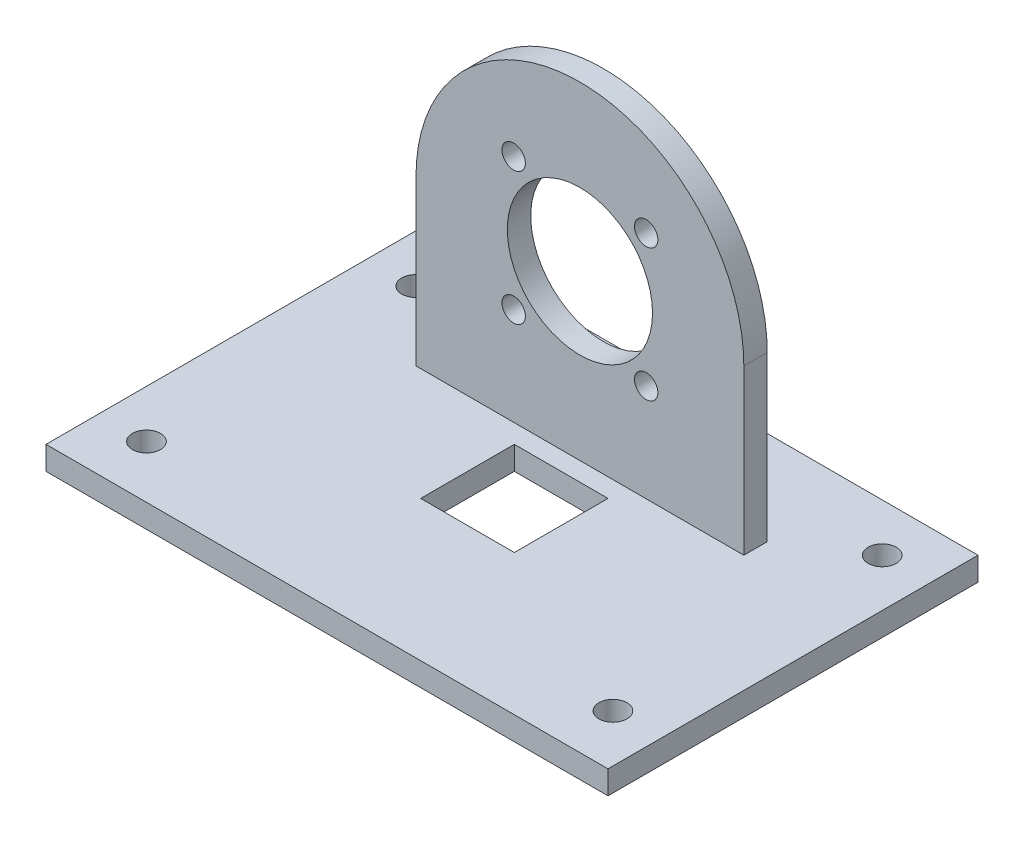
SolidWorks part; units mm, degrees
material "Alloy Steel"
ref_plane "Front Plane" through (0, 0, 0) normal (0, 0, 1) x (1, 0, 0)
ref_plane "Top Plane" through (0, 0, 0) normal (0, 1, 0) x (1, 0, 0)
ref_plane "Right Plane" through (0, 0, 0) normal (1, 0, 0) x (0, 0, -1)
sketch "Sketch1" plane through (0, 0, 0) normal (0, 1, 0) x (1, 0, 0)
  line L0 (0, -114.1661) -> (0, 132.8372) construction
  line L1 (135.7044, 0) -> (-145.1402, 0) construction
  line L2 (-35, -40) -> (-20, -40)
  line L3 (-35, 19) -> (35, 19) construction
  line L4 (-35, 19) -> (-35, -40) construction
  line L5 (-20, -70) -> (20, -70)
  line L6 (35, 19) -> (35, -40) construction
  line L7 (-20, -40) -> (-20, -70)
  line L8 (35, -40) -> (20, -40)
  line L9 (20, -40) -> (20, -70)
  line L10 (-35, -40) -> (-60, -40)
  line L11 (-60, -40) -> (-60, 39)
  line L12 (-60, 39) -> (60, 39)
  line L13 (60, 39) -> (60, -40)
  line L14 (60, -40) -> (35, -40)
  circle A0 centre (0, 0) radius 57.5 construction
  circle A1 centre (0, 0) radius 2.5 construction
  circle A2 centre (0, 57.5) radius 3 construction
  circle A3 centre (49.7965, 28.75) radius 3
  circle A4 centre (49.7965, -28.75) radius 3
  circle A5 centre (0, -57.5) radius 3
  circle A6 centre (-49.7965, -28.75) radius 3
  circle A7 centre (-49.7965, 28.75) radius 3
  point P22 (0, 0)
  dimension "D1" = 115
  dimension "D2" = 6
  dimension "D3" = 5
  dimension "D4" = 6
  dimension "D5" = 70
  dimension "D6" = 19
  dimension "D7" = 35
  dimension "D8" = 25
  dimension "D9" = 30
  dimension "D10" = 15
  dimension "D11" = 30
  dimension "D12" = 15
  dimension "D13" = 25
  dimension "D14" = 20
extrude "Boss-Extrude1" add sketch "Sketch1" along normal blind 5
sketch "Sketch2" plane through (0, 5, 0) normal (0, 1, 0) x (1, 0, 0)
  line L1 (-35, 19) -> (35, 19)
  line L2 (-35, 19) -> (-35, 14)
  line L3 (-35, 14) -> (35, 14)
  line L4 (35, 14) -> (35, 19)
  dimension "D1" = 70
  dimension "D2" = 5
  dimension "D3" = 19
extrude "Boss-Extrude2" add sketch "Sketch2" along normal blind 70
sketch "Sketch3" plane through (0, 0, -19) normal (0, 0, -1) x (-1, 0, 0)
  line L0 (-35, 75) -> (35, 75) construction
  line L1 (35, 75) -> (35, 5) construction
  line L2 (-35, 75) -> (-35, 5) construction
  line L3 (35, 75) -> (35, 40)
  line L4 (-35, 75) -> (-35, 40)
  line L5 (-35, 75) -> (35, 75)
  arc A0 (35, 40) -> (-35, 40) centre (0, 40) ccw
  line M2 (35, 5) -> (35, 75)
  line M3 (35, 75) -> (-35, 75)
  line M4 (-35, 75) -> (-35, 5)
  dimension "D1" = 70
extrude "Cut-Extrude1" cut sketch "Sketch3" against normal blind 20 contours A0 L5 M4 | A0 M2 M3
sketch "Sketch4" plane through (0, 0, -14) normal (0, 0, 1) x (1, 0, 0)
  circle A0 centre (0, 40) radius 15.5
  dimension "D1" = 31
extrude "Cut-Extrude2" cut sketch "Sketch4" against normal blind 10
sketch "Sketch8" plane through (0, 0, 0) normal (0, -1, 0) x (1, 0, 0)
  line L0 (0, 70) -> (0, 0) construction
  line L1 (-20, 70) -> (20, 70) construction
  line L3 (-10, -10) -> (10, -10)
  line L4 (-10, -10) -> (-10, 10)
  line L5 (-10, 10) -> (10, 10)
  line L6 (10, -10) -> (10, 10)
  line L7 (-10, -10) -> (10, 10) construction
  line L8 (-10, 10) -> (10, -10) construction
  dimension "D1" = 70
  dimension "D2" = 20
  dimension "D3" = 20
extrude "Cut-Extrude6" cut sketch "Sketch8" against normal up to surface (28.1573 mm away)
sketch "Sketch9" plane through (0, 0, 70) normal (0, 0, 1) x (1, 0, 0)
  line L1 (-20, 5) -> (20, 5)
  line L2 (-20, 5) -> (-20, 0)
  line L3 (-20, 0) -> (20, 0)
  line L4 (20, 5) -> (20, 0)
extrude "Cut-Extrude7" cut sketch "Sketch9" against normal up to surface (30 mm away) up to face at (40, 2.5, 40)
sketch "Sketch10" plane through (0, 0, -19) normal (0, 0, -1) x (-1, 0, 0)
  line L0 (0, 40) -> (0, 73.9404) construction
  line L1 (0, 40) -> (33.32, 73.32) construction
  circle A0 centre (0, 40) radius 20 construction
  circle A1 centre (14.1421, 54.1421) radius 2.5
  circle A2 centre (14.1421, 25.8579) radius 2.5
  circle A3 centre (-14.1421, 25.8579) radius 2.5
  circle A4 centre (-14.1421, 54.1421) radius 2.5
  point P17 (0, 40)
  dimension "D1" = 40
  dimension "D3" = 5
  dimension "D2" = 45
  dimension "D4" = 4
extrude "Cut-Extrude8" cut sketch "Sketch10" against normal up to surface (5 mm away) up to face at (15.5, 40, -14)
